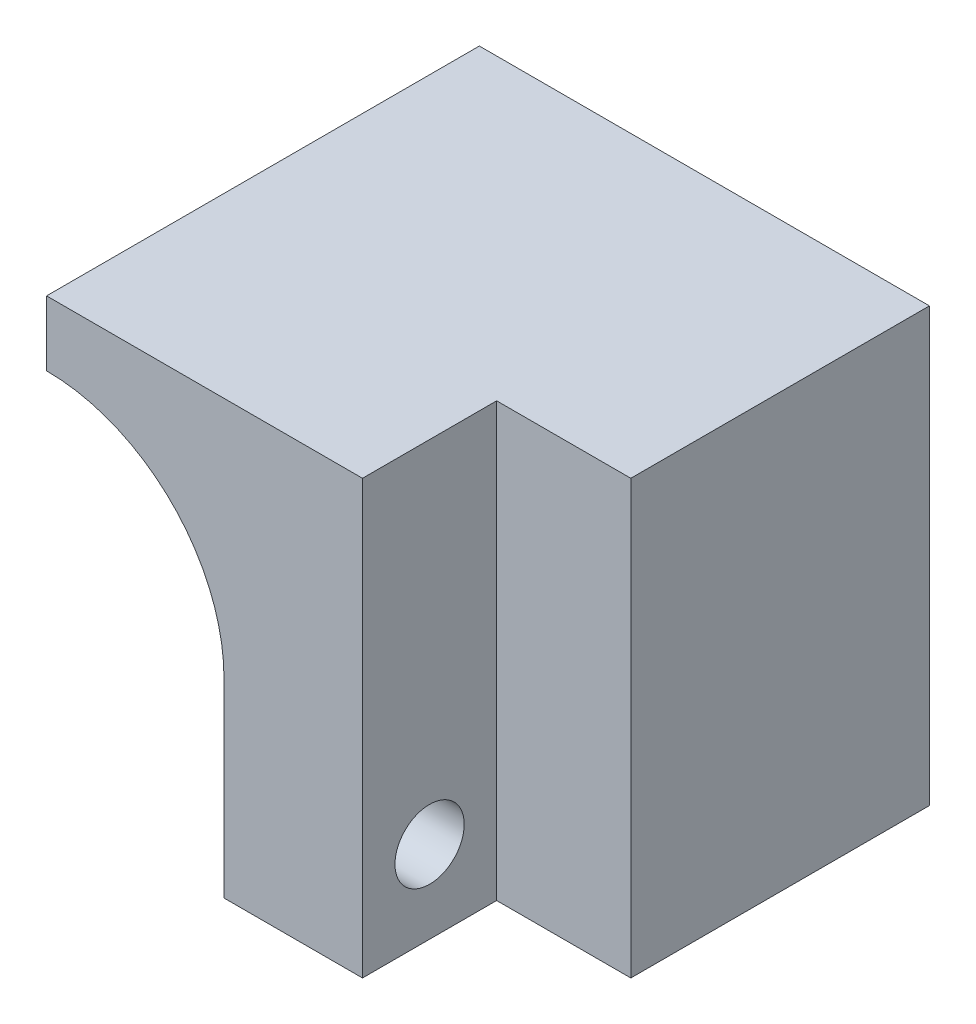
SolidWorks part; units mm, degrees
ref_plane "Alzado" through (0, 0, 0) normal (0, 0, 1) x (1, 0, 0)
ref_plane "Planta" through (0, 0, 0) normal (0, 1, 0) x (1, 0, 0)
ref_plane "Vista lateral" through (0, 0, 0) normal (1, 0, 0) x (0, 0, -1)
sketch "Croquis1" plane through (0, 0, 0) normal (0, 0, 1) x (1, 0, 0)
  line L1 (0, 0) -> (20.8, 0)
  line L2 (0, 0) -> (0, -20)
  line L3 (0, -20) -> (20.8, -20)
  line L4 (20.8, 0) -> (20.8, -20)
  dimension "D1" = 20.8
  dimension "D2" = 20
extrude "Saliente-Extruir1" add sketch "Croquis1" along normal blind 2
sketch "Croquis2" plane through (0, 0, 2) normal (0, 0, 1) x (1, 0, 0)
  line L0 (0, 0) -> (0, -20) construction
  line L1 (8.2, -11.2) -> (8.2, -20)
  line L2 (0, -20) -> (20.8, -20) construction
  line L3 (8.2, -20) -> (20.8, -20)
  line L4 (0, 0) -> (0, -20)
  line L5 (0, -20) -> (20.8, -20)
  line L6 (20.8, -20) -> (20.8, 0)
  line L7 (20.8, 0) -> (0, 0)
  line L8 (0, 0) -> (0, -3)
  line L10 (20.8, -20) -> (20.8, 0)
  line L11 (20.8, 0) -> (0, 0)
  arc A0 (0, -3) -> (8.2, -11.2) centre (0, -11.2) cw
  dimension "D2" = 8.2
  dimension "D3" = 3
  dimension "D1" = 0
extrude "Saliente-Extruir2" add sketch "Croquis2" along normal blind 11.8
sketch "Croquis3" plane through (0, 0, 13.8) normal (0, 0, 1) x (1, 0, 0)
  line L0 (14.6, -20) -> (14.6, 0)
  line L1 (20.8, -20) -> (20.8, 0) construction
  line L5 (20.8, 0) -> (0, 0)
  line L6 (0, 0) -> (0, -3)
  line L7 (8.2, -11.2) -> (8.2, -20)
  line L8 (8.2, -20) -> (20.8, -20)
  line L9 (20.8, -20) -> (20.8, 0)
  line L10 (14.6, 0) -> (0, 0)
  line L11 (0, 0) -> (0, -3)
  line L12 (8.2, -11.2) -> (8.2, -20)
  line L13 (8.2, -20) -> (14.6, -20)
  arc A1 (8.2, -11.2) -> (0, -3) centre (0, -11.2) ccw
  arc A2 (8.2, -11.2) -> (0, -3) centre (0, -11.2) ccw
  dimension "D2" = 6.2
  dimension "D1" = 0
extrude "Saliente-Extruir3" add sketch "Croquis3" along normal blind 6.2
sketch "Croquis4" plane through (14.6, 0, 0) normal (1, 0, 0) x (0, 0, -1)
  line L0 (-16.9, -20) -> (-16.9, -16.2) construction
  line L1 (-20, -20) -> (-13.8, -20) construction
  line L2 (-20, 0) -> (-13.8, 0) construction
  circle A0 centre (-16.9, -16.2) radius 1.6
  dimension "D2" = 3.2
  dimension "D1" = 16.2
extrude "Cortar-Extruir1" cut sketch "Croquis4" against normal up to next
sketch "Croquis5" plane through (8.2, 0, 0) normal (-1, 0, 0) x (0, 0, 1)
  line L1 (16.9, -19.4909) -> (19.75, -17.8454)
  line L2 (19.75, -17.8454) -> (19.75, -14.5546)
  line L3 (19.75, -14.5546) -> (16.9, -12.9091)
  line L4 (16.9, -12.9091) -> (14.05, -14.5546)
  line L5 (14.05, -14.5546) -> (14.05, -17.8454)
  line L6 (14.05, -17.8454) -> (16.9, -19.4909)
  circle A0 centre (16.9, -16.2) radius 2.85 construction
  dimension "D1" = 5.7
extrude "Cortar-Extruir2" cut sketch "Croquis5" against normal blind 3
